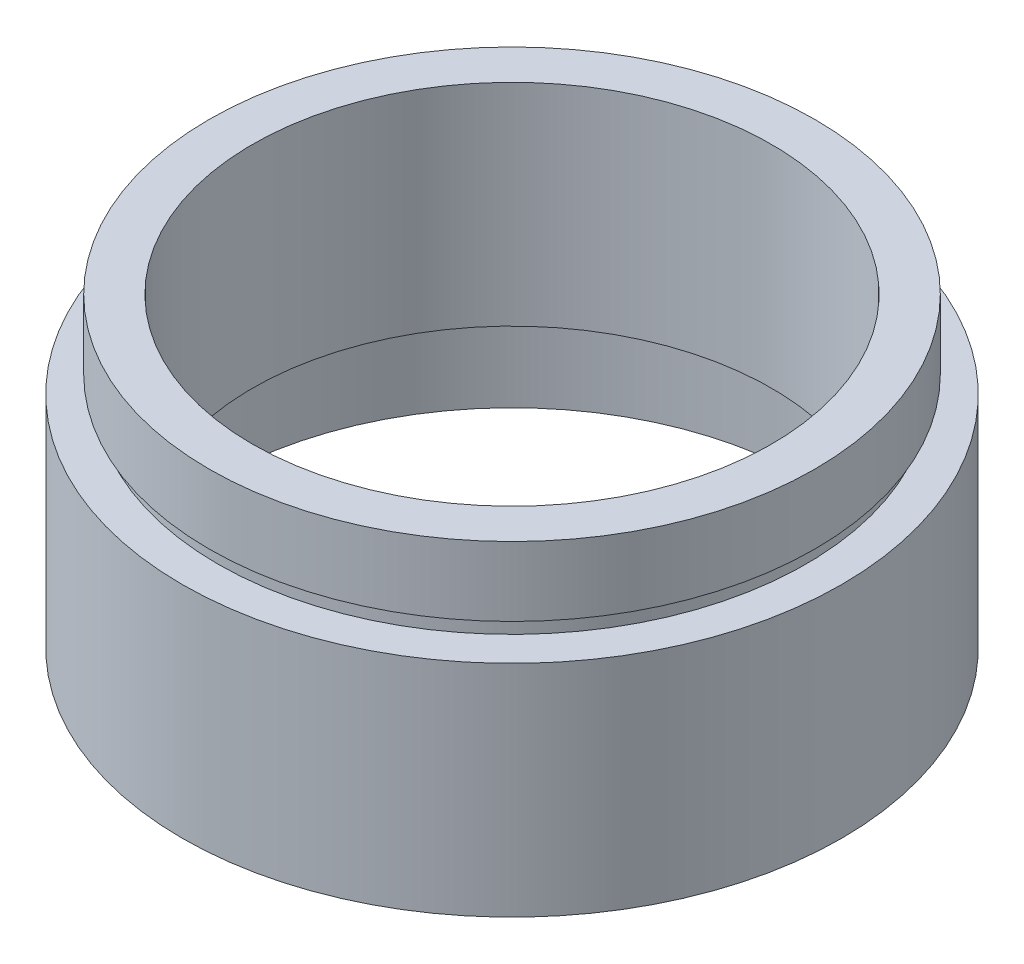
SolidWorks part; units mm, degrees
ref_plane "前视基准面" through (0, 0, 0) normal (0, 0, 1) x (1, 0, 0)
ref_plane "上视基准面" through (0, 0, 0) normal (0, 1, 0) x (1, 0, 0)
ref_plane "右视基准面" through (0, 0, 0) normal (1, 0, 0) x (0, 0, -1)
sketch "草图1" plane through (0, 0, 0) normal (0, 0, 1) x (1, 0, 0)
  line L0 (0, 161.3762) -> (0, 0) construction
  line L1 (141.7365, 0) -> (-131.7984, 0) construction
  line L2 (19.05, 0) -> (19.05, 12.7)
  line L3 (17, 4.5) -> (17.6, 4.5)
  line L4 (17, 0) -> (19.05, 0)
  line L5 (17.6, 4.5) -> (17.6, 5.5)
  line L6 (15, 5.5) -> (15, 17.7)
  line L7 (17, 4.5) -> (17, 0)
  line L8 (17.6, 5.5) -> (15, 5.5)
  line L9 (17, 13.7) -> (17, 12.7)
  line L10 (19.05, 12.7) -> (17, 12.7)
  line L11 (17.5, 13.7) -> (17.5, 17.7)
  line L12 (17, 13.7) -> (17.5, 13.7)
  line L13 (17.5, 17.7) -> (15, 17.7)
  dimension "D2" = 19.05
  dimension "D3" = 17.6
  dimension "D4" = 15
  dimension "D5" = 17
  dimension "D6" = 17.5
  dimension "D7" = 1
  dimension "D8" = 12.7
  dimension "D9" = 5
  dimension "D10" = 1
  dimension "D11" = 17
revolve "旋转1" add sketch "草图1" angle 360 about L0
cosmetic thread "装饰螺纹线1" parameters "D2"=35
cosmetic thread "装饰螺纹线2" parameters "D2"=31
cosmetic thread "装饰螺纹线3" parameters "D2"=34
